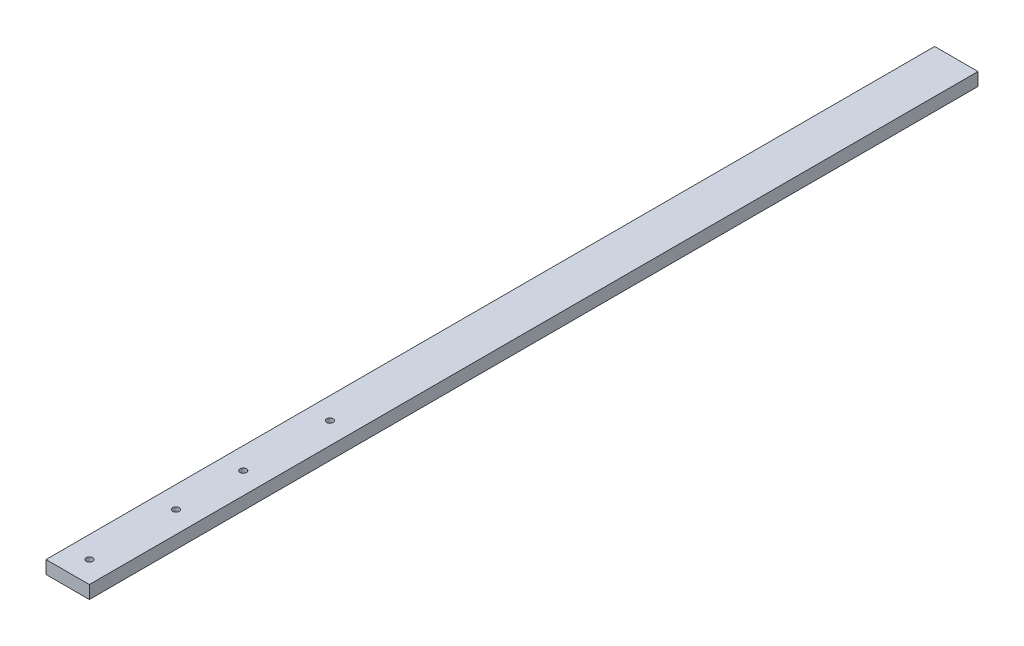
SolidWorks part; units mm, degrees
material "Pine"
ref_plane "Front Plane" through (0, 0, 0) normal (0, 0, 1) x (1, 0, 0)
ref_plane "Top Plane" through (0, 0, 0) normal (0, 1, 0) x (1, 0, 0)
ref_plane "Right Plane" through (0, 0, 0) normal (1, 0, 0) x (0, 0, -1)
sketch "Sketch1" plane through (0, 0, 0) normal (0, 1, 0) x (1, 0, 0)
  line L1 (10, -205) -> (-10, -205)
  line L2 (10, -205) -> (10, 205)
  line L3 (10, 205) -> (-10, 205)
  line L4 (-10, -205) -> (-10, 205)
  line L5 (10, -205) -> (-10, 205) construction
  line L6 (10, 205) -> (-10, -205) construction
  point P0 (0, 0)
  dimension "D1" = 20
  dimension "D2" = 410
extrude "Boss-Extrude1" add sketch "Sketch1" along normal blind 6
sketch "Sketch2" plane through (0, 6, 0) normal (0, 1, 0) x (1, 0, 0)
  line L0 (-10, -205) -> (10, -205) construction
  circle A0 centre (0, -195) radius 1.5
  circle A1 centre (0, -155) radius 1.5
  circle A2 centre (0, -124) radius 1.5
  circle A3 centre (0, -84) radius 1.5
  dimension "D1" = 3
  dimension "D3" = 3
  dimension "D8" = 3
  dimension "D9" = 3
  dimension "D4" = 40
  dimension "D5" = 10
  dimension "D6" = 31
  dimension "D7" = 40
extrude "Cut-Extrude1" cut sketch "Sketch2" against normal through all
